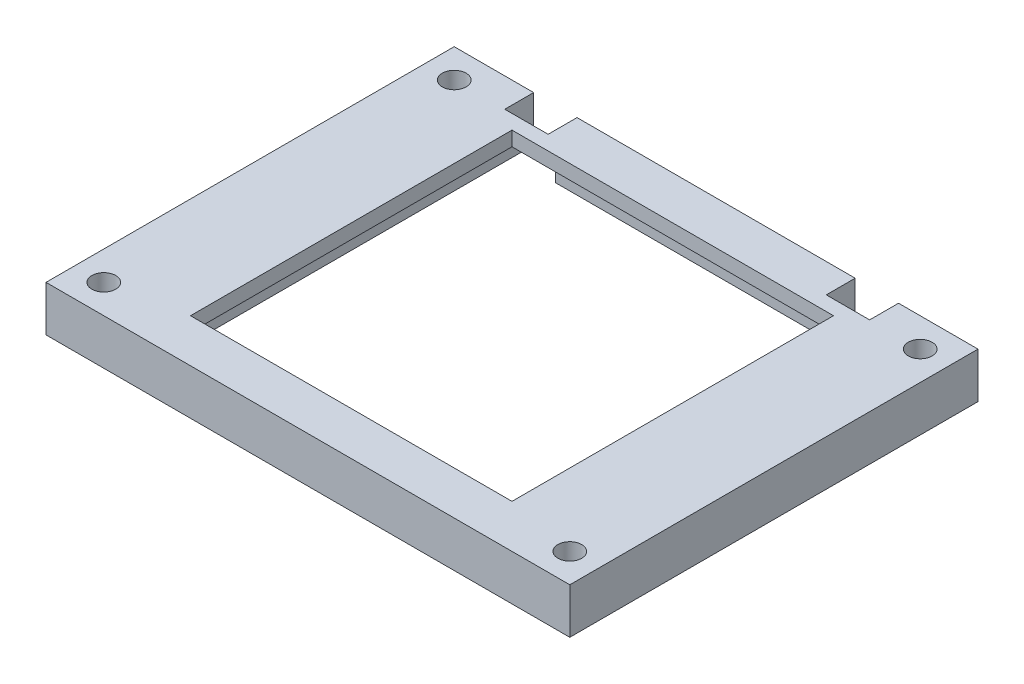
SolidWorks part; units mm, degrees
ref_plane "Front Plane" through (0, 0, 0) normal (0, 0, 1) x (1, 0, 0)
ref_plane "Top Plane" through (0, 0, 0) normal (0, 1, 0) x (1, 0, 0)
ref_plane "Right Plane" through (0, 0, 0) normal (1, 0, 0) x (0, 0, -1)
sketch "Sketch1" plane through (0, 0, 0) normal (0, 1, 0) x (1, 0, 0)
  line L0 (-28.25, 12.25) -> (-36.25, 20.25)
  line L1 (-25.25, 25.25) -> (25.25, 25.25)
  line L2 (-25.25, 25.25) -> (-25.25, -25.25)
  line L3 (-25.25, -25.25) -> (25.25, -25.25)
  line L4 (25.25, 25.25) -> (25.25, -25.25)
  line L5 (-25.25, 25.25) -> (25.25, -25.25) construction
  line L6 (-25.25, -25.25) -> (25.25, 25.25) construction
  line L7 (-28.25, 28.25) -> (28.25, 28.25)
  line L8 (-28.25, 28.25) -> (-28.25, -28.25)
  line L9 (-28.25, -28.25) -> (28.25, -28.25)
  line L10 (28.25, 28.25) -> (28.25, -28.25)
  line L11 (-28.25, 28.25) -> (28.25, -28.25) construction
  line L12 (-28.25, -28.25) -> (28.25, 28.25) construction
  line L13 (-36.25, 20.25) -> (-36.25, 30.25)
  line L14 (-36.25, 30.25) -> (-32.25, 34.25)
  line L15 (-32.25, 34.25) -> (-24.25, 34.25)
  line L16 (-24.25, 34.25) -> (-18.25, 28.25)
  line L17 (-3.465, 0) -> (3.465, 0) construction
  line L18 (-28.25, -12.25) -> (-36.25, -20.25)
  line L19 (-24.25, -34.25) -> (-18.25, -28.25)
  line L20 (-32.25, -34.25) -> (-24.25, -34.25)
  line L21 (-36.25, -30.25) -> (-32.25, -34.25)
  line L22 (-36.25, -20.25) -> (-36.25, -30.25)
  line L23 (0, -3.465) -> (0, 3.465) construction
  line L24 (32.25, -34.25) -> (24.25, -34.25)
  line L25 (24.25, -34.25) -> (18.25, -28.25)
  line L26 (28.25, -12.25) -> (36.25, -20.25)
  line L27 (36.25, -20.25) -> (36.25, -30.25)
  line L28 (36.25, -30.25) -> (32.25, -34.25)
  line L29 (24.25, 34.25) -> (18.25, 28.25)
  line L30 (32.25, 34.25) -> (24.25, 34.25)
  line L31 (36.25, 30.25) -> (32.25, 34.25)
  line L32 (36.25, 20.25) -> (36.25, 30.25)
  line L33 (28.25, 12.25) -> (36.25, 20.25)
  circle A0 centre (-32.25, 24.25) radius 1.65
  circle A1 centre (-32.25, -24.25) radius 1.65
  circle A2 centre (32.25, -24.25) radius 1.65
  circle A3 centre (32.25, 24.25) radius 1.65
  point P0 (0, 0)
  point P5 (0, 0)
  dimension "D11" = 3.3
  dimension "D12" = 4
  dimension "D1" = 50.5
  dimension "D2" = 50.5
  dimension "D3" = 56.5
  dimension "D4" = 6
  dimension "D5" = 8
  dimension "D6" = 4
  dimension "D7" = 8
  dimension "D8" = 4
  dimension "D9" = 4
  dimension "D10" = 45
  dimension "D13" = 4
extrude "Boss-Extrude1" add sketch "Sketch1" along normal blind 8.6 contours L10 L7 L8 L9 L1 L4 L3 L2 | L18 L22 L21 L20 L19 L9 L8 A1 | L28 L27 L26 L10 L9 L25 L24 A2 | L10 L33 L32 L31 L30 L29 L7 A3 | L16 L15 L14 L13 L0 L8 L7 A0
sketch "Sketch2" plane through (0, 0, 0) normal (0, 1, 0) x (1, 0, 0)
  line L1 (-25.25, 25.25) -> (25.25, 25.25)
  line L2 (-25.25, 25.25) -> (-25.25, -25.25)
  line L3 (-25.25, -25.25) -> (25.25, -25.25)
  line L4 (25.25, 25.25) -> (25.25, -25.25)
  line L5 (-25.25, 25.25) -> (25.25, -25.25) construction
  line L6 (-25.25, -25.25) -> (25.25, 25.25) construction
  line L7 (-22.25, 22.25) -> (22.25, 22.25)
  line L8 (-22.25, 22.25) -> (-22.25, -22.25)
  line L9 (-22.25, -22.25) -> (22.25, -22.25)
  line L10 (22.25, 22.25) -> (22.25, -22.25)
  line L11 (-22.25, 22.25) -> (22.25, -22.25) construction
  line L12 (-22.25, -22.25) -> (22.25, 22.25) construction
  point P0 (0, 0)
  point P5 (0, 0)
  dimension "D1" = 50.5
  dimension "D2" = 50.5
  dimension "D3" = 44.5
  dimension "D4" = 44.5
extrude "Boss-Extrude2" add sketch "Sketch2" along normal blind 2
sketch "Sketch4" plane through (0, 0, 0) normal (0, 1, 0) x (1, 0, 0)
  line L1 (-25.25, 25.25) -> (25.25, 25.25)
  line L2 (-25.25, 25.25) -> (-25.25, -25.25)
  line L3 (-25.25, -25.25) -> (25.25, -25.25)
  line L4 (25.25, 25.25) -> (25.25, -25.25)
  line L5 (-25.25, 25.25) -> (25.25, -25.25) construction
  line L6 (-25.25, -25.25) -> (25.25, 25.25) construction
  line L7 (-22.25, 22.25) -> (22.25, 22.25)
  line L8 (-22.25, 22.25) -> (-22.25, -22.25)
  line L9 (-22.25, -22.25) -> (22.25, -22.25)
  line L10 (22.25, 22.25) -> (22.25, -22.25)
  line L11 (-22.25, 22.25) -> (22.25, -22.25) construction
  line L12 (-22.25, -22.25) -> (22.25, 22.25) construction
  point P0 (0, 0)
  point P5 (0, 0)
extrude "Boss-Extrude3" add sketch "Sketch4" along normal blind 2 from offset 6.6
sketch "Sketch5" plane through (0, 0, 0) normal (0, 1, 0) x (1, 0, 0)
  line L1 (-25.25, 19.8891) -> (-19.25, 19.8891)
  line L2 (-25.25, 19.8891) -> (-25.25, 37.8505)
  line L3 (-25.25, 37.8505) -> (-19.25, 37.8505)
  line L4 (-19.25, 19.8891) -> (-19.25, 37.8505)
  line L5 (19.25, 19.8891) -> (25.25, 19.8891)
  line L6 (19.25, 19.8891) -> (19.25, 37.8505)
  line L7 (19.25, 37.8505) -> (25.25, 37.8505)
  line L8 (25.25, 19.8891) -> (25.25, 37.8505)
  dimension "D1" = 6
  dimension "D2" = 6
  dimension "D3" = 25.25
  dimension "D4" = 25.25
extrude "Cut-Extrude1" cut sketch "Sketch5" along normal blind 4.6 from offset 2
sketch "Sketch6" plane through (0, 0, 0) normal (0, -1, 0) x (1, 0, 0)
  line L1 (-41.762, 39.56) -> (45.5585, 39.56)
  line L2 (-41.762, 39.56) -> (-41.762, -42.5972)
  line L3 (-41.762, -42.5972) -> (45.5585, -42.5972)
  line L4 (45.5585, 39.56) -> (45.5585, -42.5972)
extrude "Cut-Extrude2" cut sketch "Sketch6" against normal blind 2.3
sketch "Sketch7" plane through (0, 8.6, 0) normal (0, 1, 0) x (1, 0, 0)
  line L0 (-18.25, 28.25) -> (18.25, 28.25) construction
  line L1 (-36.25, 20.25) -> (-28.25, 20.25)
  line L2 (-36.25, 20.25) -> (-36.25, -20.25)
  line L3 (-36.25, -20.25) -> (-28.25, -20.25)
  line L4 (-28.25, 20.25) -> (-28.25, -20.25)
  line L5 (36.25, 20.25) -> (28.25, 20.25)
  line L6 (36.25, 20.25) -> (36.25, -20.25)
  line L7 (36.25, -20.25) -> (28.25, -20.25)
  line L8 (28.25, 20.25) -> (28.25, -20.25)
  line L9 (0, 28.25) -> (-38.2076, 28.25)
  line L10 (0, 28.25) -> (0, 36.7246)
  line L11 (0, 36.7246) -> (-38.2076, 36.7246)
  line L12 (-38.2076, 28.25) -> (-38.2076, 36.7246)
  line L13 (-18.25, -28.25) -> (18.25, -28.25) construction
  line L14 (0, 28.25) -> (40.9812, 28.25)
  line L15 (0, 28.25) -> (0, 36.7246)
  line L16 (0, 36.7246) -> (40.9812, 36.7246)
  line L17 (40.9812, 28.25) -> (40.9812, 36.7246)
  line L18 (0, -28.25) -> (-40.8818, -28.25)
  line L19 (0, -28.25) -> (0, -34.9953)
  line L20 (0, -34.9953) -> (-40.8818, -34.9953)
  line L21 (-40.8818, -28.25) -> (-40.8818, -34.9953)
  line L23 (0, -28.25) -> (39.1843, -28.25)
  line L24 (0, -28.25) -> (0, -34.9953)
  line L25 (0, -34.9953) -> (39.1843, -34.9953)
  line L26 (39.1843, -28.25) -> (39.1843, -34.9953)
  line M1 (28.25, -12.25) -> (28.25, 12.25)
  line M2 (28.25, 12.25) -> (36.25, 20.25)
  line M3 (36.25, 20.25) -> (36.25, 30.25)
  line M4 (36.25, 30.25) -> (32.25, 34.25)
  line M5 (32.25, 34.25) -> (24.25, 34.25)
  line M6 (24.25, 34.25) -> (18.25, 28.25)
  line M7 (18.25, 28.25) -> (-18.25, 28.25)
  line M8 (-18.25, 28.25) -> (-24.25, 34.25)
  line M9 (-24.25, 34.25) -> (-32.25, 34.25)
  line M10 (-32.25, 34.25) -> (-36.25, 30.25)
  line M11 (-36.25, 30.25) -> (-36.25, 20.25)
  line M12 (-36.25, 20.25) -> (-28.25, 12.25)
  line M13 (-28.25, 12.25) -> (-28.25, -12.25)
  line M14 (-28.25, -12.25) -> (-36.25, -20.25)
  line M15 (-36.25, -20.25) -> (-36.25, -30.25)
  line M16 (-36.25, -30.25) -> (-32.25, -34.25)
  line M17 (-32.25, -34.25) -> (-24.25, -34.25)
  line M18 (-24.25, -34.25) -> (-18.25, -28.25)
  line M19 (-18.25, -28.25) -> (18.25, -28.25)
  line M20 (18.25, -28.25) -> (24.25, -34.25)
  line M21 (24.25, -34.25) -> (32.25, -34.25)
  line M22 (32.25, -34.25) -> (36.25, -30.25)
  line M23 (36.25, -30.25) -> (36.25, -20.25)
  line M24 (36.25, -20.25) -> (28.25, -12.25)
extrude "Cut-Extrude4" cut sketch "Sketch7" against normal blind 10 contours L18 L21 L20 L19 M19 M18 M17 M16 M15 | L26 L23 L19 L25 M23 M22 M21 M20 M19 | L6 M2 M1 M24 | L2 M12 M14 M13 | L9 M8 M9 M10 M11 | L12 L9 L10 L11 M11 M10 M9 M8 M7 | L5 L8 M2 | L8 L7 M24 | L18 M18 M15 M16 M17 | L4 L3 M14 | L4 L1 M12 | L14 M6 M3 M4 M5 | L14 L17 L16 L10 M7 M6 M5 M4 M3 | L23 M20 M21 M22 M23
sketch "Sketch8" plane through (0, 8.6, 0) normal (0, 1, 0) x (1, 0, 0)
  line L1 (-36.25, 20.25) -> (-28.25, 20.25)
  line L2 (-36.25, 20.25) -> (-36.25, -20.25)
  line L3 (-36.25, -20.25) -> (-28.25, -20.25)
  line L4 (-28.25, 20.25) -> (-28.25, -20.25)
  line L5 (28.25, -20.25) -> (36.25, -20.25)
  line L6 (28.25, -20.25) -> (28.25, 20.25)
  line L7 (28.25, 20.25) -> (36.25, 20.25)
  line L8 (36.25, -20.25) -> (36.25, 20.25)
extrude "Boss-Extrude4" add sketch "Sketch8" against normal up to vertex (6.3 mm away) up to point (-36.25, 2.3, 20.25)
sketch "Sketch9" plane through (0, 0, -28.25) normal (0, 0, -1) x (-1, 0, 0)
  line L0 (36.25, 8.6) -> (-36.25, 8.6) construction
  line L1 (-25.25, 2.3) -> (-19.25, 2.3)
  line L2 (-25.25, 2.3) -> (-25.25, 8.6)
  line L3 (-25.25, 8.6) -> (-19.25, 8.6)
  line L4 (-19.25, 2.3) -> (-19.25, 8.6)
  line L5 (19.25, 2.3) -> (25.25, 2.3)
  line L6 (19.25, 2.3) -> (19.25, 8.6)
  line L7 (19.25, 8.6) -> (25.25, 8.6)
  line L8 (25.25, 2.3) -> (25.25, 8.6)
  point P12 (-19.2324, 8.6)
  point P13 (-19.25, 2.3)
  point P15 (25.25, 2.3)
extrude "Cut-Extrude5" cut sketch "Sketch9" against normal blind 4
